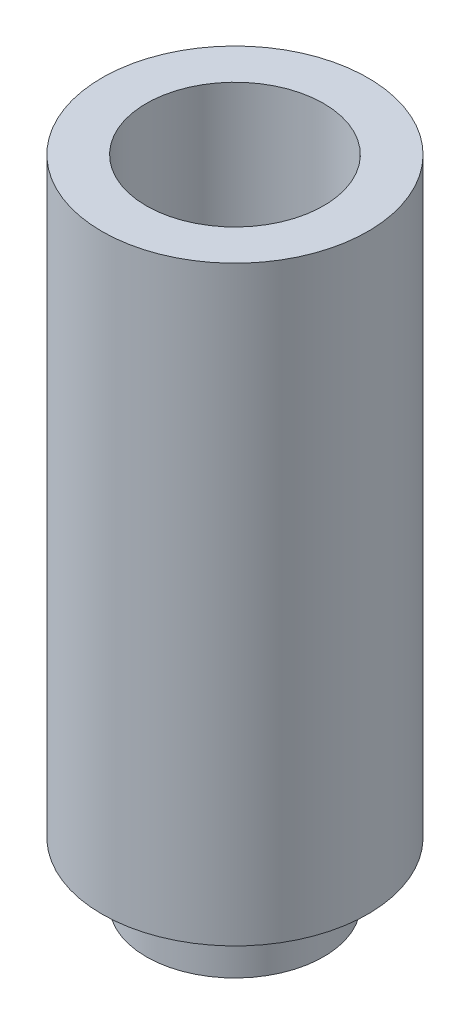
SolidWorks part; units mm, degrees
ref_plane "Front Plane" through (0, 0, 0) normal (0, 0, 1) x (1, 0, 0)
ref_plane "Top Plane" through (0, 0, 0) normal (0, 1, 0) x (1, 0, 0)
ref_plane "Right Plane" through (0, 0, 0) normal (1, 0, 0) x (0, 0, -1)
sketch "Sketch1" plane through (0, 0, 0) normal (0, 1, 0) x (1, 0, 0)
  circle A0 centre (0, 0) radius 6
extrude "Boss-Extrude1" add sketch "Sketch1" along normal blind 4
sketch "Sketch2" plane through (0, 4, 0) normal (0, 1, 0) x (1, 0, 0)
  circle A0 centre (0, 0) radius 9
extrude "Boss-Extrude2" add sketch "Sketch2" along normal blind 40
sketch "Sketch3" plane through (0, 0, 0) normal (0, -1, 0) x (1, 0, 0)
  circle A0 centre (0, 0) radius 3.5
extrude "Cut-Extrude1" cut sketch "Sketch3" against normal blind 4
sketch "Sketch4" plane through (0, 44, 0) normal (0, 1, 0) x (1, 0, 0)
  circle A0 centre (0, 0) radius 6
extrude "Cut-Extrude2" cut sketch "Sketch4" against normal blind 10
